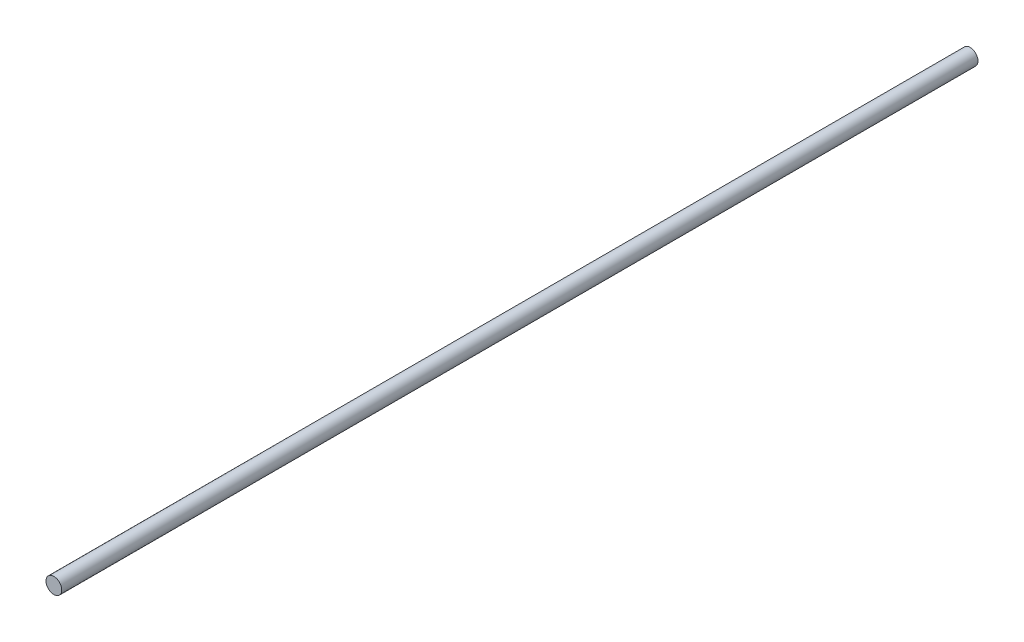
SolidWorks part; units mm, degrees
ref_plane "前视基准面" through (0, 0, 0) normal (0, 0, 1) x (1, 0, 0)
ref_plane "上视基准面" through (0, 0, 0) normal (0, 1, 0) x (1, 0, 0)
ref_plane "右视基准面" through (0, 0, 0) normal (1, 0, 0) x (0, 0, -1)
sketch "草图1" plane through (0, 0, 0) normal (0, 0, 1) x (1, 0, 0)
  circle A0 centre (0, 0) radius 4
  dimension "D1" = 8
extrude "凸台-拉伸1" add sketch "草图1" along normal blind 465
